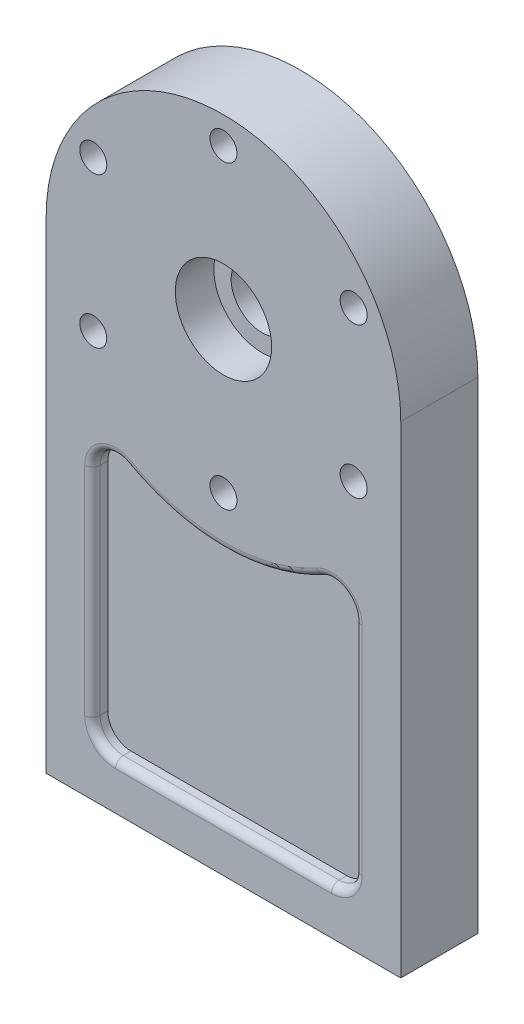
SolidWorks part; units mm, degrees
ref_plane "Front Plane" through (0, 0, 0) normal (0, 0, 1) x (1, 0, 0)
ref_plane "Top Plane" through (0, 0, 0) normal (0, 1, 0) x (1, 0, 0)
ref_plane "Right Plane" through (0, 0, 0) normal (1, 0, 0) x (0, 0, -1)
sketch "Sketch1" plane through (0, 0, 0) normal (0, 0, 1) x (1, 0, 0)
  line L0 (46, 0) -> (-46, 0) construction
  line L1 (-46, 0) -> (-46, -125)
  line L2 (-46, -125) -> (46, -125)
  line L3 (46, -125) -> (46, 0)
  arc A0 (-46, 0) -> (46, 0) centre (0, 0) cw
  circle A2 centre (0, 0) radius 8
  point P4 (0, 0)
  dimension "D3" = 16
  dimension "D1" = 92
  dimension "D2" = 125
extrude "Boss-Extrude1" add sketch "Sketch1" along normal mid plane 20
sketch "Sketch2" plane through (0, 0, 10) normal (0, 0, 1) x (1, 0, 0)
  circle A0 centre (0, 0) radius 12.5
  dimension "D1" = 25
extrude "Cut-Extrude1" cut sketch "Sketch2" against normal blind 10
sketch "Sketch3" plane through (0, 0, 10) normal (0, 0, 1) x (1, 0, 0)
  circle A0 centre (0, 0) radius 39 construction
  circle A1 centre (0, 39) radius 3.5
  circle A2 centre (0, 0) radius 39 construction
  circle A3 centre (33.775, 19.5) radius 3.5
  circle A4 centre (0, 0) radius 39 construction
  circle A5 centre (33.775, -19.5) radius 3.5
  circle A6 centre (0, 0) radius 39 construction
  circle A7 centre (0, -39) radius 3.5
  circle A8 centre (0, 0) radius 39 construction
  circle A9 centre (-33.775, -19.5) radius 3.5
  circle A10 centre (0, 0) radius 39 construction
  circle A11 centre (-33.775, 19.5) radius 3.5
  point P23 (0, 0)
  dimension "D1" = 78
  dimension "D2" = 7
  dimension "D3" = 6
extrude "Cut-Extrude2" cut sketch "Sketch3" against normal through all
sketch "Sketch4" plane through (0, 0, -10) normal (0, 0, -1) x (-1, 0, 0)
  circle A0 centre (0, 0) radius 39 construction
  circle A1 centre (0, 39) radius 6
  circle A2 centre (0, 0) radius 39 construction
  circle A3 centre (33.775, 19.5) radius 6
  circle A4 centre (0, 0) radius 39 construction
  circle A5 centre (33.775, -19.5) radius 6
  circle A6 centre (0, 0) radius 39 construction
  circle A7 centre (0, -39) radius 6
  circle A8 centre (0, 0) radius 39 construction
  circle A9 centre (-33.775, -19.5) radius 6
  circle A10 centre (0, 0) radius 39 construction
  circle A11 centre (-33.775, 19.5) radius 6
  point P2 (0, 0)
  point P5 (0, 0)
  point P23 (0, 0)
  dimension "D1" = 78
  dimension "D2" = 12
  dimension "D3" = 6
extrude "Cut-Extrude3" cut sketch "Sketch4" against normal blind 6
sketch "Sketch5" plane through (0, 0, 10) normal (0, 0, 1) x (1, 0, 0)
  line L0 (-34, -50.7937) -> (-34, -107)
  line L1 (-28, -113) -> (28, -113)
  line L2 (34, -107) -> (34, -50.7937)
  line L3 (-46, 0) -> (-46, -125) construction
  line L5 (-46, -125) -> (46, -125) construction
  arc A0 (-25.1034, -45.5392) -> (25.1034, -45.5392) centre (0, 0) ccw
  arc A1 (28, -113) -> (34, -107) centre (28, -107) ccw
  arc A2 (-34, -107) -> (-28, -113) centre (-28, -107) ccw
  arc A3 (-34, -50.7937) -> (-25.1034, -45.5392) centre (-28, -50.7937) cw
  arc A4 (34, -50.7937) -> (25.1034, -45.5392) centre (28, -50.7937) ccw
  dimension "D1" = 52
  dimension "D3" = 6
  dimension "D2" = 12
  dimension "D4" = 12
extrude "Cut-Extrude4" cut sketch "Sketch5" against normal blind 4
fillet "Fillet1" radius 2 8 edges at (-31.0513, -45.6275, 10) (0, -52, 10) (31.0513, -45.6275, 10) (34, -78.8969, 10) (32.2426, -111.2426, 10) (0, -113, 10) (-32.2426, -111.2426, 10) (-34, -78.8969, 10)
hole_wizard "Tap Drill for M10x1.25 Tap1" positions "Sketch8" profile "Sketch9" hole size "M10x1.25" standard "ISO"
sketch "Sketch8" plane through (0, -125, 0) normal (0, -1, 0) x (-1, 0, 0)
  line L0 (46, -10) -> (46, 10) construction
  line L1 (46, 10) -> (-46, 10) construction
  point P0 (30, 0)
  point P2 (-30, 0)
  dimension "D1" = 60
  dimension "D2" = 16
  dimension "D3" = 10
sketch "Sketch9" plane through (-30, -125, 0) normal (1, 0, 0) x (0, 0, -1)
  line L0 (0, 0) -> (0, 15.6438)
  line L1 (0, 15.6438) -> (4.4, 13)
  line L2 (4.4, 13) -> (4.4, 0.025)
  line L3 (4.4, 0.025) -> (4.425, 0)
  line L5 (4.425, 0) -> (0, 0)
  line L6 (-4.4, 0.025) -> (-4.425, 0) construction
  line L10 (0, 15.6438) -> (-4.4, 13) construction
  line L11 (0, -6.35) -> (0, 107.95) construction
  dimension "Hole Dia." = 8.8
  dimension "Hole Depth" = 13
  dimension "Near C'Sink Dia." = 8.85
  dimension "Near C'Sink Angle" = 90
  dimension "Drill Angle" = 118
mirror "Mirror4" about plane through (0, 0, 0) normal (0, 0, 1) of "Fillet1", "Cut-Extrude4"
